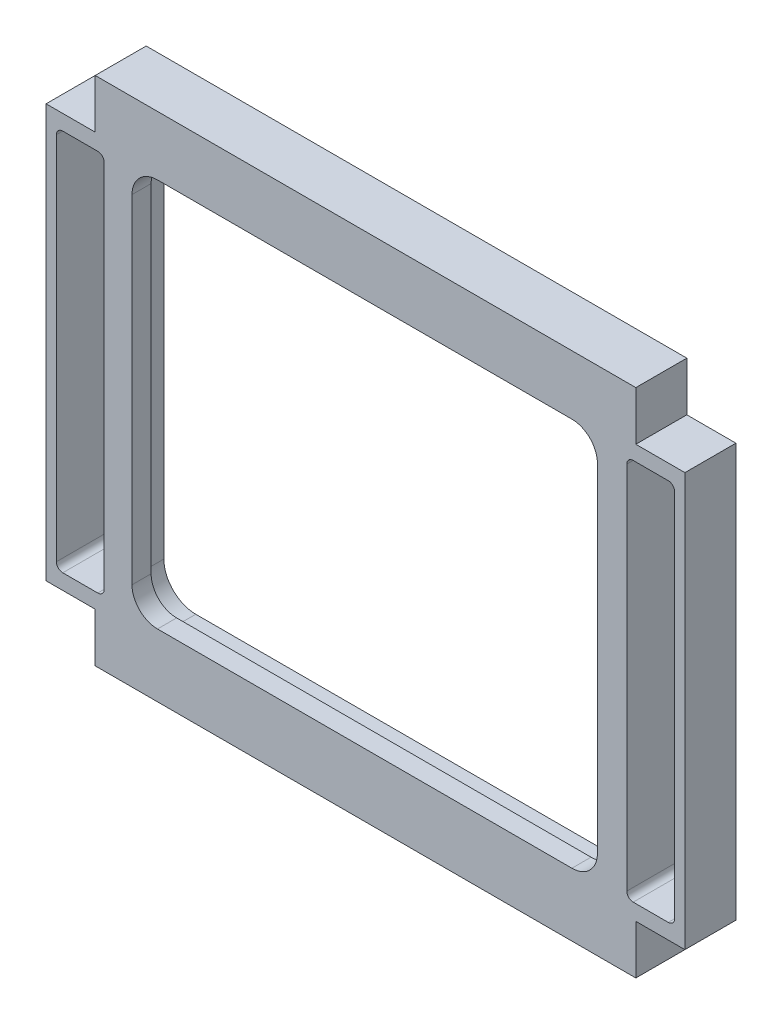
SolidWorks part; units mm, degrees
ref_plane "Plan de face" through (0, 0, 0) normal (0, 0, 1) x (1, 0, 0)
ref_plane "Plan de dessus" through (0, 0, 0) normal (0, 1, 0) x (1, 0, 0)
ref_plane "Plan de droite" through (0, 0, 0) normal (1, 0, 0) x (0, 0, -1)
sketch "Esquisse1" plane through (0, 0, 0) normal (0, 0, 1) x (1, 0, 0)
  line L4 (-47.9586, -0.2167) -> (52.2414, -0.2167) construction
  line L5 (-40.2586, 39.8833) -> (44.5414, 39.8833)
  line L6 (-47.9586, 32.1833) -> (-47.9586, -32.6167)
  line L7 (-40.2586, -40.3167) -> (44.5414, -40.3167)
  line L8 (52.2414, 32.1833) -> (52.2414, -32.6167)
  line L11 (-47.9586, 32.1833) -> (-40.2586, 32.1833)
  line L12 (-40.2586, 39.8833) -> (-40.2586, 32.1833)
  line L13 (2.1414, 39.8833) -> (2.1414, -40.3167) construction
  line L14 (44.5414, 39.8833) -> (44.5414, 32.1833)
  line L15 (52.2414, 32.1833) -> (44.5414, 32.1833)
  line L16 (52.2414, -32.6167) -> (44.5414, -32.6167)
  line L17 (44.5414, -40.3167) -> (44.5414, -32.6167)
  line L18 (-40.2586, -40.3167) -> (-40.2586, -32.6167)
  line L19 (-47.9586, -32.6167) -> (-40.2586, -32.6167)
  line L20 (-32.4836, 33.5833) -> (36.5164, 33.5833)
  line L21 (41.5164, 28.5833) -> (41.5164, -28.4167)
  line L22 (36.5164, -33.4167) -> (-32.4836, -33.4167)
  line L23 (-37.4836, -28.4167) -> (-37.4836, 28.5833)
  line L24 (2.0164, 33.5833) -> (2.0164, -33.4167) construction
  line L25 (-37.4836, 0.0833) -> (41.5164, 0.0833) construction
  line L26 (-37.4836, 28.5833) -> (41.5164, 28.5833) construction
  line L27 (-37.4836, -28.4167) -> (41.5164, -28.4167) construction
  arc A4 (36.5164, 33.5833) -> (41.5164, 28.5833) centre (36.5164, 28.5833) cw
  arc A5 (41.5164, -28.4167) -> (36.5164, -33.4167) centre (36.5164, -28.4167) cw
  arc A6 (-32.4836, -33.4167) -> (-37.4836, -28.4167) centre (-32.4836, -28.4167) cw
  arc A7 (-37.4836, 28.5833) -> (-32.4836, 33.5833) centre (-32.4836, 28.5833) cw
  point P0 (2.0164, 33.5833)
  point P6 (2.1414, -0.2167)
  point P7 (0, 0)
  dimension "D9" = 5
  dimension "D10" = 5
  dimension "D1" = 69
  dimension "D2" = 57
  dimension "D3" = 57
  dimension "D4" = 69
  dimension "D5" = 7.7
  dimension "D6" = 7.7
  dimension "D7" = 84.8
  dimension "D8" = 64.8
extrude "Boss.-Extru.1" add sketch "Esquisse1" along normal blind 5
sketch "Esquisse2" plane through (0, 0, 5) normal (0, 0, 1) x (1, 0, 0)
  line L0 (-47.9586, 32.1833) -> (-40.2586, 32.1833)
  line L1 (-40.2586, 32.1833) -> (-40.2586, 39.8833)
  line L2 (-40.2586, 39.8833) -> (44.5414, 39.8833)
  line L3 (44.5414, 39.8833) -> (44.5414, 32.1833)
  line L4 (44.5414, 32.1833) -> (52.2414, 32.1833)
  line L5 (52.2414, 32.1833) -> (52.2414, -32.6167)
  line L6 (52.2414, -32.6167) -> (44.5414, -32.6167)
  line L7 (44.5414, -32.6167) -> (44.5414, -40.3167)
  line L8 (44.5414, -40.3167) -> (-40.2586, -40.3167)
  line L9 (-40.2586, -40.3167) -> (-40.2586, -32.6167)
  line L10 (-40.2586, -32.6167) -> (-47.9586, -32.6167)
  line L11 (-47.9586, -32.6167) -> (-47.9586, 32.1833)
extrude "Boss.-Extru.2" add sketch "Esquisse2" along normal blind 3
sketch "Esquisse8" plane through (0, 0, 5) normal (0, 0, -1) x (-1, 0, 0)
  line L0 (-36.5164, 33.5833) -> (32.4836, 33.5833) construction
  line L3 (-34.5164, 30.5833) -> (30.4836, 30.5833)
  line L6 (-38.5164, 26.5833) -> (-38.5164, -26.4167)
  line L7 (-34.5164, -30.4167) -> (30.4836, -30.4167)
  line L8 (34.4836, 26.5833) -> (34.4836, -26.4167)
  line L10 (37.4836, 28.5833) -> (37.4836, -28.4167) construction
  line L11 (32.4836, -33.4167) -> (-36.5164, -33.4167) construction
  line L12 (-41.5164, -28.4167) -> (-41.5164, 28.5833) construction
  arc A0 (-34.5164, -30.4167) -> (-38.5164, -26.4167) centre (-34.5164, -26.4167) cw
  arc A1 (34.4836, -26.4167) -> (30.4836, -30.4167) centre (30.4836, -26.4167) cw
  arc A2 (30.4836, 30.5833) -> (34.4836, 26.5833) centre (30.4836, 26.5833) cw
  arc A3 (-38.5164, 26.5833) -> (-34.5164, 30.5833) centre (-34.5164, 26.5833) cw
  dimension "D3" = 3
  dimension "D5" = 4
  dimension "D1" = 3
  dimension "D2" = 3
  dimension "D4" = 3
extrude "Enlèv. mat.-Extru.9" cut sketch "Esquisse8" against normal blind 10
sketch "Esquisse6" plane through (0, 0, 0) normal (0, 0, -1) x (-1, 0, 0)
  line L0 (-2.1414, 39.8833) -> (-2.1414, -40.3167) construction
  line L1 (-49.6289, 29.7833) -> (-44.1289, 29.7833)
  line L2 (-50.6289, 28.7833) -> (-50.6289, -29.2167)
  line L3 (-49.6289, -30.2167) -> (-44.1289, -30.2167)
  line L4 (-43.1289, 28.7833) -> (-43.1289, -29.2167)
  line L5 (-44.5414, 39.8833) -> (40.2586, 39.8833) construction
  line L6 (40.2586, -40.3167) -> (-44.5414, -40.3167) construction
  line L10 (-52.2414, 32.1833) -> (-41.5164, 32.1833) construction
  line L13 (-50.6289, -0.2167) -> (-43.1289, -0.2167) construction
  line L14 (45.3461, -30.2167) -> (39.8461, -30.2167)
  line L15 (38.8461, 28.7833) -> (38.8461, -29.2167)
  line L16 (45.3461, 29.7833) -> (39.8461, 29.7833)
  line L17 (46.3461, 28.7833) -> (46.3461, -29.2167)
  arc A0 (-49.6289, -30.2167) -> (-50.6289, -29.2167) centre (-49.6289, -29.2167) cw
  arc A1 (-44.1289, -30.2167) -> (-43.1289, -29.2167) centre (-44.1289, -29.2167) ccw
  arc A2 (-44.1289, 29.7833) -> (-43.1289, 28.7833) centre (-44.1289, 28.7833) cw
  arc A3 (-49.6289, 29.7833) -> (-50.6289, 28.7833) centre (-49.6289, 28.7833) ccw
  arc A4 (39.8461, -30.2167) -> (38.8461, -29.2167) centre (39.8461, -29.2167) cw
  arc A5 (39.8461, 29.7833) -> (38.8461, 28.7833) centre (39.8461, 28.7833) ccw
  arc A6 (45.3461, -30.2167) -> (46.3461, -29.2167) centre (45.3461, -29.2167) ccw
  arc A7 (45.3461, 29.7833) -> (46.3461, 28.7833) centre (45.3461, 28.7833) cw
  point P16 (-50.6289, -0.2167)
  point P23 (-46.8789, -0.2167)
  point P26 (-50.6289, -30.2167)
  point P31 (-43.1289, 29.7833)
  point P34 (-50.6289, 29.7833)
  point P47 (0, 0)
  dimension "D3" = 1
  dimension "D1" = 7.5
  dimension "D2" = 60
extrude "Enlèv. mat.-Extru.4" cut sketch "Esquisse6" against normal through all
